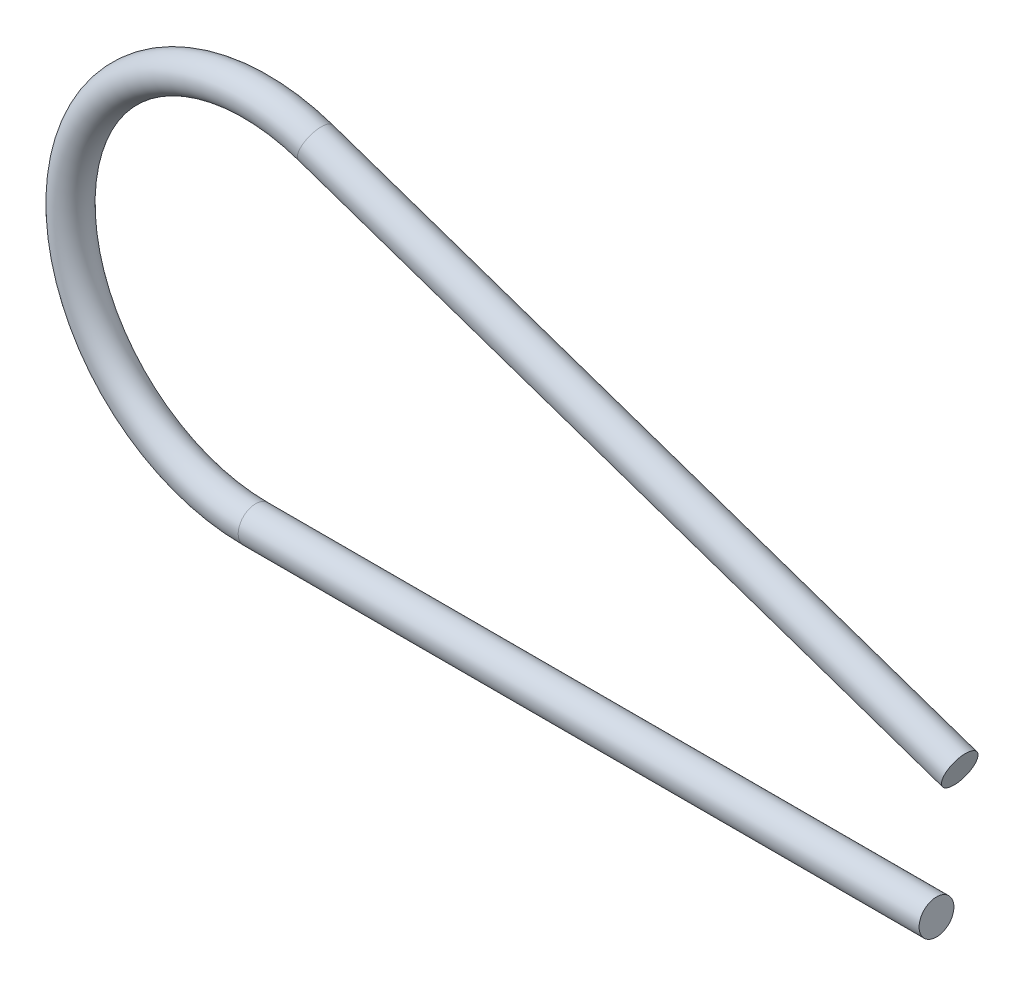
SolidWorks part; units mm, degrees
ref_plane "Alzado" through (0, 0, 0) normal (0, 0, 1) x (1, 0, 0)
ref_plane "Planta" through (0, 0, 0) normal (0, 1, 0) x (1, 0, 0)
ref_plane "Vista lateral" through (0, 0, 0) normal (1, 0, 0) x (0, 0, -1)
sketch "Sketch1" plane through (0, 0, 0) normal (0, 0, 1) x (1, 0, 0)
  line L0 (-1000, 0) -> (49000, 0) construction
  line L1 (0, -1000) -> (0, 49000) construction
  line L2 (-5.3528, 3.1056) -> (0.2004, 1.203)
  line L3 (-5.87, 0) -> (0, 0)
  line L4 (-5.3041, 3.2475) -> (0.249, 1.3449) construction
  circle A0 centre (-5.87, 1.5959) radius 1.5959 construction
  arc A1 (-5.3528, 3.1056) -> (-5.87, 0) centre (-5.87, 1.5959) ccw
  arc A2 (-1.5377, 2.0044) -> (-0.551, 1.8594) centre (-0.9018, 2.9019) ccw construction
  point P2 (-5.87, 0)
  point P4 (-5.87, 1.5959)
  point P15 (-10.7427, 1.5837)
  dimension "D1" = 5.87
  dimension "D2" = 5.5403
  dimension "D3" = 5.87
  dimension "D4" = 0.15
curve "CompCurve1"
sketch "Sketch2" plane through (0, 0, 0) normal (1, 0, 0) x (0, 0, -1)
  circle A0 centre (0, 0) radius 0.15
  dimension "D1" = 0.3
sweep "Sweep1" add profiles "Sketch2" path "CompCurve1"
